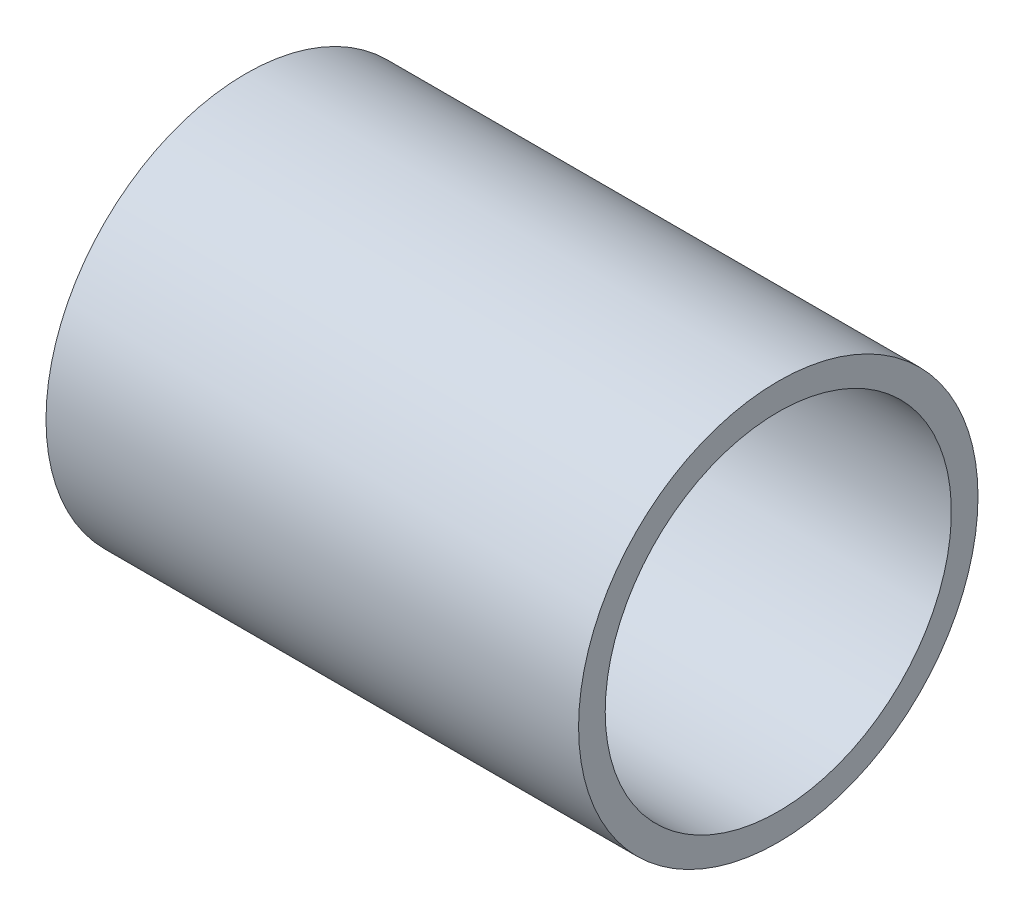
SolidWorks part; units mm, degrees
ref_plane "Front Plane" through (0, 0, 0) normal (0, 0, 1) x (1, 0, 0)
ref_plane "Top Plane" through (0, 0, 0) normal (0, 1, 0) x (1, 0, 0)
ref_plane "Right Plane" through (0, 0, 0) normal (1, 0, 0) x (0, 0, -1)
sketch "Sketch1" plane through (0, 0, 0) normal (0, 1, 0) x (1, 0, 0)
  line L0 (0, 0) -> (120.629, 0)
  line L4 (0, -82.55) -> (254, -82.55)
  dimension "D1" = 82.55
revolve "Revolve-Thin2" add sketch "Sketch1" angle 360 about L0
